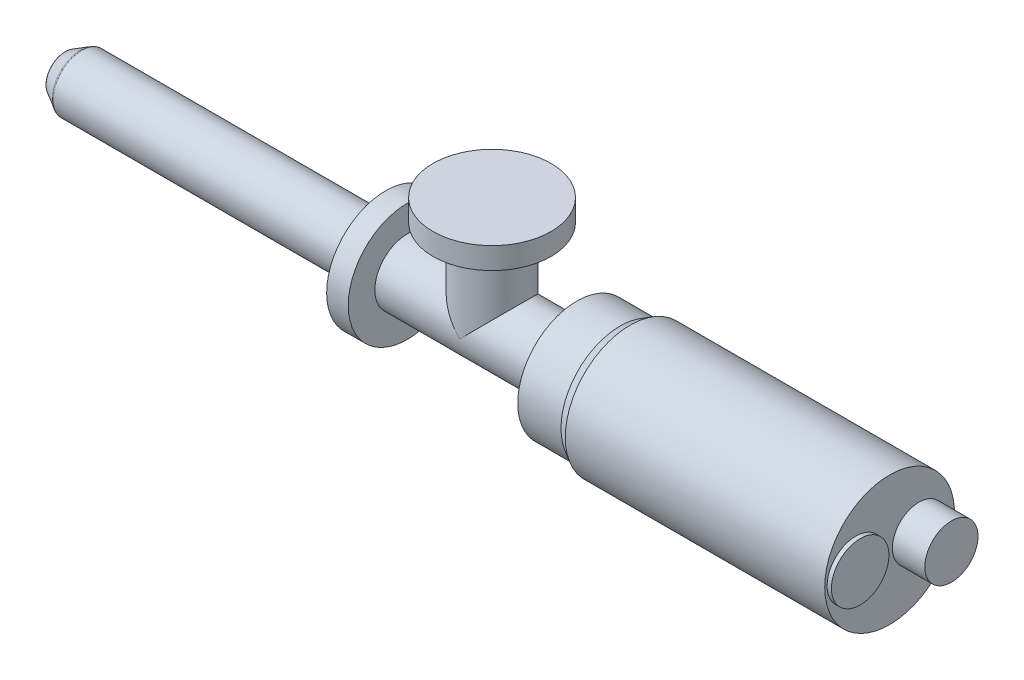
SolidWorks part; units mm, degrees
ref_plane "Front Plane" through (0, 0, 0) normal (0, 0, 1) x (1, 0, 0)
ref_plane "Top Plane" through (0, 0, 0) normal (0, 1, 0) x (1, 0, 0)
ref_plane "Right Plane" through (0, 0, 0) normal (1, 0, 0) x (0, 0, -1)
sketch "Sketch1" plane through (0, 0, 0) normal (0, 0, 1) x (1, 0, 0)
  line L0 (0, 0) -> (1031.9175, 0) construction
  line L1 (0, 0) -> (0, 11.049)
  line L2 (0, 11.049) -> (9.7227, 16.6624)
  line L3 (9.7227, 16.6624) -> (188.722, 16.6624)
  line L4 (188.722, 16.6624) -> (188.722, 34.671)
  line L5 (188.722, 34.671) -> (201.422, 34.671)
  line L6 (201.422, 34.671) -> (201.422, 19.05)
  line L7 (201.422, 19.05) -> (300.99, 19.05)
  line L8 (300.99, 19.05) -> (300.99, 34.671)
  line L9 (300.99, 34.671) -> (326.39, 34.671)
  line L10 (326.39, 34.671) -> (332.3292, 38.1)
  line L11 (332.3292, 38.1) -> (484.7292, 38.1)
  line L12 (484.7292, 38.1) -> (484.7292, 0)
  line L13 (0, 0) -> (484.7292, 0)
  dimension "D1" = 11.049
  dimension "D2" = 30
  dimension "D3" = 16.6624
  dimension "D4" = 188.722
  dimension "D5" = 12.7
  dimension "D6" = 34.671
  dimension "D7" = 99.568
  dimension "D8" = 25.4
  dimension "D9" = 34.671
  dimension "D10" = 30
  dimension "D11" = 38.1
  dimension "D12" = 152.4
  dimension "D13" = 19.05
revolve "Revolve1" add sketch "Sketch1" angle 360 about L0
sketch "Sketch2" plane through (0, 0, 0) normal (0, 1, 0) x (1, 0, 0)
  line L0 (188.722, 34.671) -> (188.722, -34.671) construction
  circle A0 centre (251.206, 0) radius 19.05
  dimension "D1" = 38.1
  dimension "D2" = 62.484
extrude "Boss-Extrude1" add sketch "Sketch2" along normal blind 62.484
sketch "Sketch3" plane through (0, 62.484, 0) normal (0, 1, 0) x (1, 0, 0)
  circle A0 centre (251.206, 0) radius 34.671
  dimension "D1" = 69.342
extrude "Boss-Extrude2" add sketch "Sketch3" against normal blind 12.7
sketch "Sketch4" plane through (484.7292, 0, 0) normal (1, 0, 0) x (0, 0, -1)
  circle A0 centre (17.272, 0) radius 15.621
  dimension "D1" = 31.242
  dimension "D2" = 0
  dimension "D3" = 17.272
extrude "Boss-Extrude3" add sketch "Sketch4" along normal blind 19.05
sketch "Sketch5" plane through (484.7292, 0, 0) normal (1, 0, 0) x (0, 0, -1)
  circle A0 centre (-19.812, 0) radius 16.891
  dimension "D2" = 33.782
  dimension "D1" = 0
  dimension "D3" = 19.812
extrude "Boss-Extrude4" add sketch "Sketch5" along normal blind 2.54
fillet "Fillet1" radius 1.524 2 edges at (9.7227, 0, 16.6624) (0, 0, 11.049)
sketch "Sketch6" plane through (0, 0, 0) normal (-1, 0, 0) x (0, 0, 1)
  circle A0 centre (0, 0) radius 3.175
  dimension "D1" = 6.35
extrude "Cut-Extrude1" cut sketch "Sketch6" against normal blind 12.7
